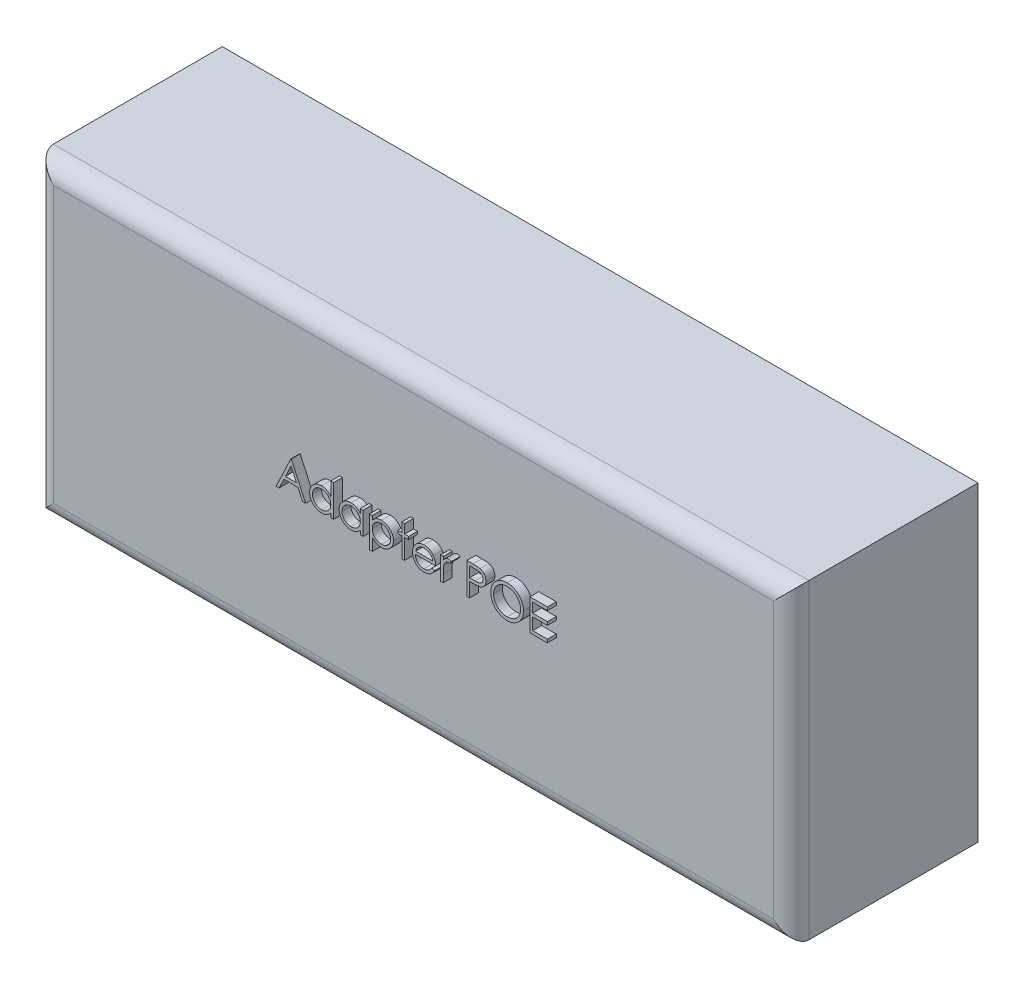
SolidWorks part; units mm, degrees
ref_plane "Front Plane" through (0, 0, 0) normal (0, 0, 1) x (1, 0, 0)
ref_plane "Top Plane" through (0, 0, 0) normal (0, 1, 0) x (1, 0, 0)
ref_plane "Right Plane" through (0, 0, 0) normal (1, 0, 0) x (0, 0, -1)
sketch "Sketch1" plane through (0, 0, 0) normal (0, 0, 1) x (1, 0, 0)
  line L1 (-42.5, -17.5) -> (42.5, -17.5)
  line L2 (-42.5, -17.5) -> (-42.5, 17.5)
  line L3 (-42.5, 17.5) -> (42.5, 17.5)
  line L4 (42.5, -17.5) -> (42.5, 17.5)
  line L5 (0, 17.5) -> (0, -17.5) construction
  line L6 (-42.5, 0) -> (42.5, 0) construction
  point P0 (0, 0)
  point P4 (63, 0)
  dimension "D1" = 85
  dimension "D2" = 35
extrude "Boss-Extrude1" add sketch "Sketch1" along normal blind 21
fillet "Fillet1" radius 2 4 edges at (0, -17.5, 21) (-42.5, 0, 21) (0, 17.5, 21) (42.5, 0, 21)
sketch "Sketch2" plane through (0, 0, 21) normal (0, 0, 1) x (1, 0, 0)
  text T0 "Adapter POE"
extrude "Boss-Extrude2" add sketch "Sketch2" along normal blind 1
